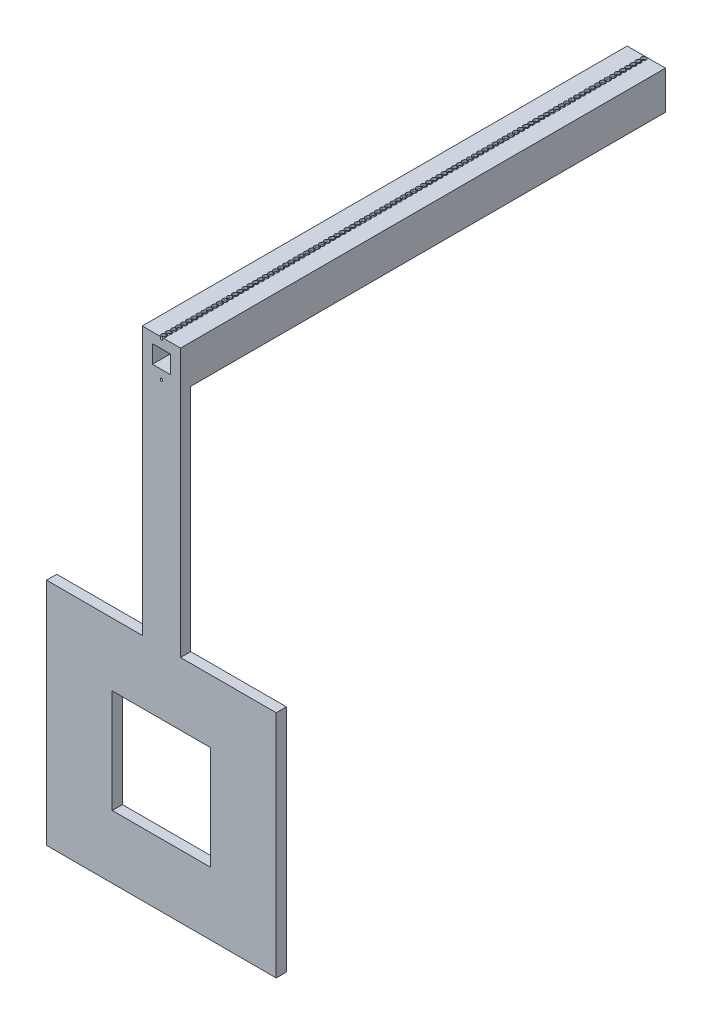
SolidWorks part; units mm, degrees
ref_plane "Front Plane" through (0, 0, 0) normal (0, 0, 1) x (1, 0, 0)
ref_plane "Top Plane" through (0, 0, 0) normal (0, 1, 0) x (1, 0, 0)
ref_plane "Right Plane" through (0, 0, 0) normal (1, 0, 0) x (0, 0, -1)
sketch "Sketch1" plane through (0, 0, 0) normal (0, 0, 1) x (1, 0, 0)
  line L0 (-1.75, 1.75) -> (-1.75, -1.75)
  line L1 (-3.75, 3.75) -> (3.75, 3.75)
  line L2 (-3.75, 3.75) -> (-3.75, -3.75)
  line L3 (-3.75, -3.75) -> (3.75, -3.75)
  line L4 (3.75, 3.75) -> (3.75, -3.75)
  line L5 (-3.75, 3.75) -> (3.75, -3.75) construction
  line L6 (-3.75, -3.75) -> (3.75, 3.75) construction
  line L7 (-1.75, -1.75) -> (1.75, -1.75)
  line L8 (1.75, 1.75) -> (1.75, -1.75)
  line L9 (-1.75, 1.75) -> (1.75, 1.75)
  point P0 (0, 0)
  dimension "D1" = 7.5
  dimension "D2" = 7.5
  dimension "D3" = 2
extrude "Boss-Extrude1" add sketch "Sketch1" along normal blind 95
sketch "Sketch2" plane through (0, 0, 95) normal (0, 0, 1) x (1, 0, 0)
  line L1 (-3.75, 3.75) -> (3.75, 3.75)
  line L2 (-3.75, 3.75) -> (-3.75, -16.25)
  line L3 (-3.75, -3.75) -> (3.75, -3.75) construction
  line L4 (3.75, 3.75) -> (3.75, -31.25)
  line L5 (-22.5, -48.75) -> (22.5, -48.75)
  line L6 (-22.5, -48.75) -> (-22.5, -93.75)
  line L7 (-22.5, -93.75) -> (22.5, -93.75)
  line L8 (22.5, -48.75) -> (22.5, -93.75)
  line L9 (-22.5, -48.75) -> (22.5, -93.75) construction
  line L10 (-22.5, -93.75) -> (22.5, -48.75) construction
  line L11 (-3.75, -16.25) -> (-3.75, -48.75)
  line L12 (3.75, -31.25) -> (3.75, -48.75)
  line L13 (-9.6324, -61.1039) -> (9.6324, -61.1039)
  line L14 (-9.6324, -61.1039) -> (-9.6324, -81.3961)
  line L15 (-9.6324, -81.3961) -> (9.6324, -81.3961)
  line L16 (9.6324, -61.1039) -> (9.6324, -81.3961)
  line L17 (-9.6324, -61.1039) -> (9.6324, -81.3961) construction
  line L18 (-9.6324, -81.3961) -> (9.6324, -61.1039) construction
  line L20 (3.75, -3.75) -> (3.75, 3.75) construction
  point P5 (0, -71.25)
  point P14 (0, -71.25)
  dimension "D1" = 0
  dimension "D2" = 45
  dimension "D3" = 45
  dimension "D4" = 0
  dimension "D5" = 45
extrude "Boss-Extrude2" add sketch "Sketch2" against normal blind 2
sketch "Sketch5" plane through (0, 3.75, 0) normal (0, 1, 0) x (1, 0, 0)
  circle A0 centre (0, -0.5428) radius 0.5051
extrude "Cut-Extrude2" cut sketch "Sketch5" against normal blind 0.5
pattern_linear "LPattern1" count 100 spacing 1 along (0, 0, 1) of "Cut-Extrude2"
mirror "Mirror1" about plane through (0, 0, 0) normal (0, 1, 0) of "LPattern1", "Cut-Extrude2"
sketch "Sketch6" plane through (0, -3.75, 0) normal (0, -1, 0) x (1, 0, 0)
  line L0 (-3.75, 93) -> (-3.75, 0) construction
  line L1 (3.75, 93) -> (-3.75, 93)
  line L2 (3.75, 93) -> (3.75, 100.6442)
  line L3 (3.75, 100.6442) -> (-3.75, 100.6442)
  line L4 (-3.75, 93) -> (-3.75, 100.6442)
